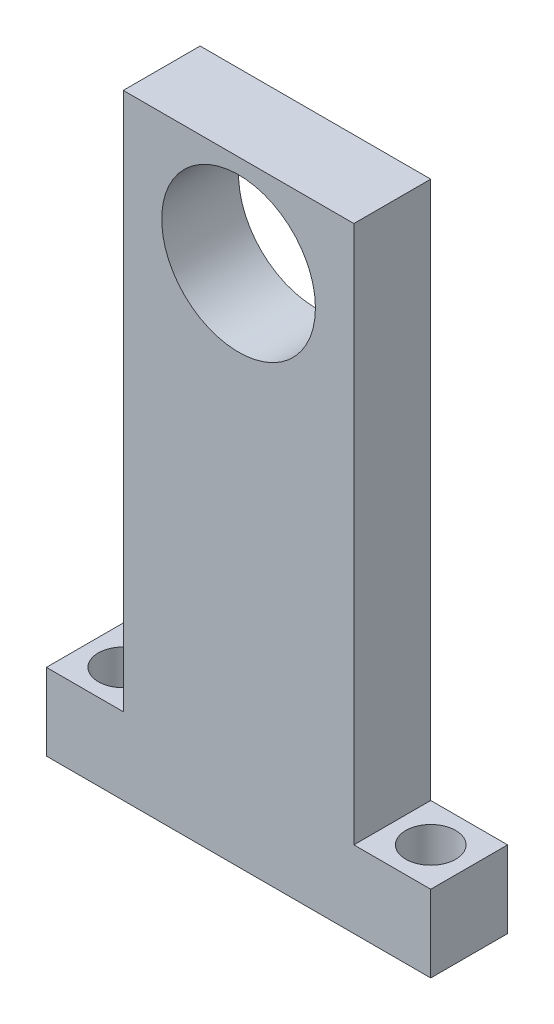
SolidWorks part; units mm, degrees
ref_plane "Front Plane" through (0, 0, 0) normal (0, 0, 1) x (1, 0, 0)
ref_plane "Top Plane" through (0, 0, 0) normal (0, 1, 0) x (1, 0, 0)
ref_plane "Right Plane" through (0, 0, 0) normal (1, 0, 0) x (0, 0, -1)
sketch "Sketch1" plane through (0, 0, 0) normal (0, 0, 1) x (1, 0, 0)
  line L1 (-15, 40) -> (15, 40)
  line L2 (-15, 40) -> (-15, -40)
  line L3 (-15, -40) -> (15, -40)
  line L4 (15, 40) -> (15, -40)
  line L5 (0, -40) -> (0, 40) construction
  line L6 (-15, 0) -> (15, 0) construction
  circle A0 centre (0, 28) radius 10
  point P0 (0, 0)
  dimension "D3" = 20
  dimension "D4" = 12
  dimension "D1" = 30
  dimension "D2" = 80
extrude "Boss-Extrude1" add sketch "Sketch1" along normal mid plane 10
sketch "Sketch2" plane through (0, -40, 0) normal (0, -1, 0) x (1, 0, 0)
  line L0 (-15, -5) -> (15, -5) construction
  line L1 (15, 5) -> (25, 5)
  line L2 (15, 5) -> (15, -5)
  line L3 (15, -5) -> (25, -5)
  line L4 (25, 5) -> (25, -5)
  line L5 (20, -5) -> (20, 5) construction
  line L6 (15, 0) -> (25, 0) construction
  circle A0 centre (20, 0) radius 3.25
  point P148 (20, 0)
  dimension "D2" = 6.5
  dimension "D1" = 10
extrude "Boss-Extrude2" add sketch "Sketch2" against normal blind 10
mirror "Mirror1" about plane through (0, 0, 0) normal (1, 0, 0) of "Boss-Extrude2"
